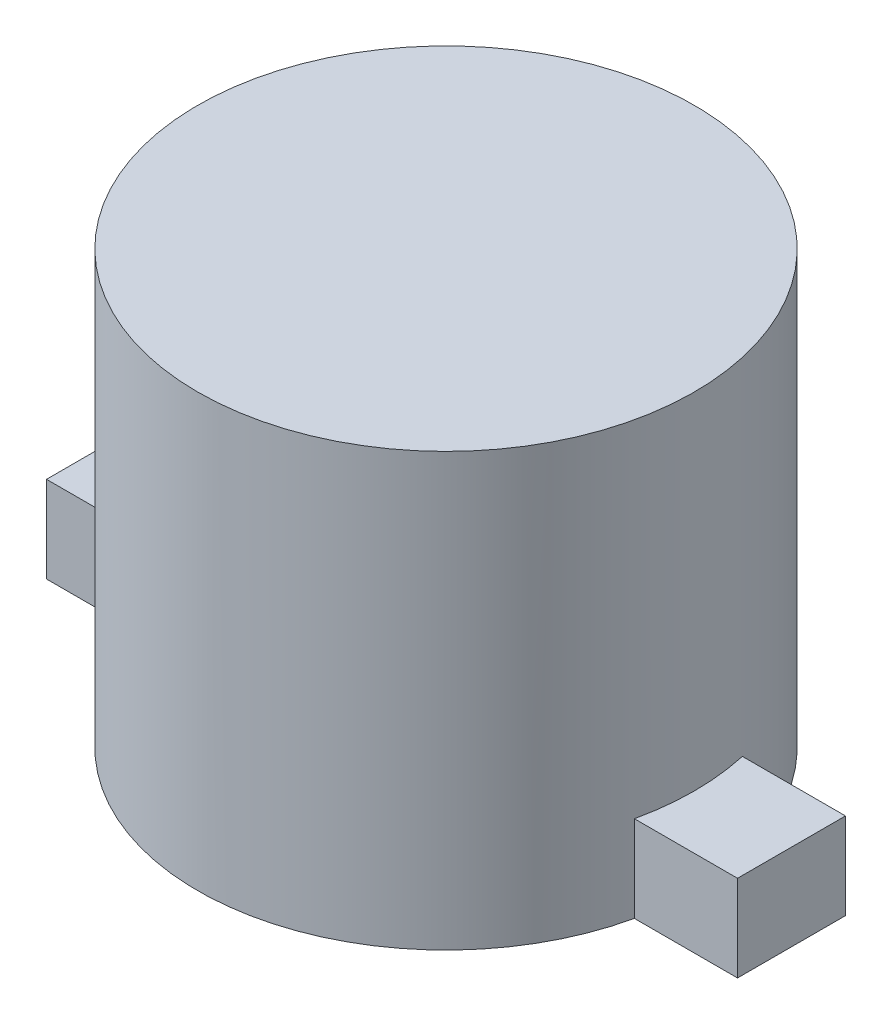
SolidWorks part; units mm, degrees
ref_plane "Front Plane" through (0, 0, 0) normal (0, 0, 1) x (1, 0, 0)
ref_plane "Top Plane" through (0, 0, 0) normal (0, 1, 0) x (1, 0, 0)
ref_plane "Right Plane" through (0, 0, 0) normal (1, 0, 0) x (0, 0, -1)
sketch "Sketch1" plane through (0, 0, 0) normal (0, 1, 0) x (1, 0, 0)
  circle A0 centre (0, 0) radius 5.75
  dimension "D1" = 11.5
extrude "Boss-Extrude1" add sketch "Sketch1" along normal blind 10
sketch "Sketch2" plane through (0, 0, 0) normal (0, -1, 0) x (-1, 0, 0)
  line L1 (8, -1.25) -> (-8, -1.25)
  line L2 (8, -1.25) -> (8, 1.25)
  line L3 (8, 1.25) -> (-8, 1.25)
  line L4 (-8, -1.25) -> (-8, 1.25)
  line L5 (8, -1.25) -> (-8, 1.25) construction
  line L6 (8, 1.25) -> (-8, -1.25) construction
  point P0 (0, 0)
  dimension "D1" = 16
  dimension "D2" = 2.5
extrude "Boss-Extrude2" add sketch "Sketch2" against normal blind 2
